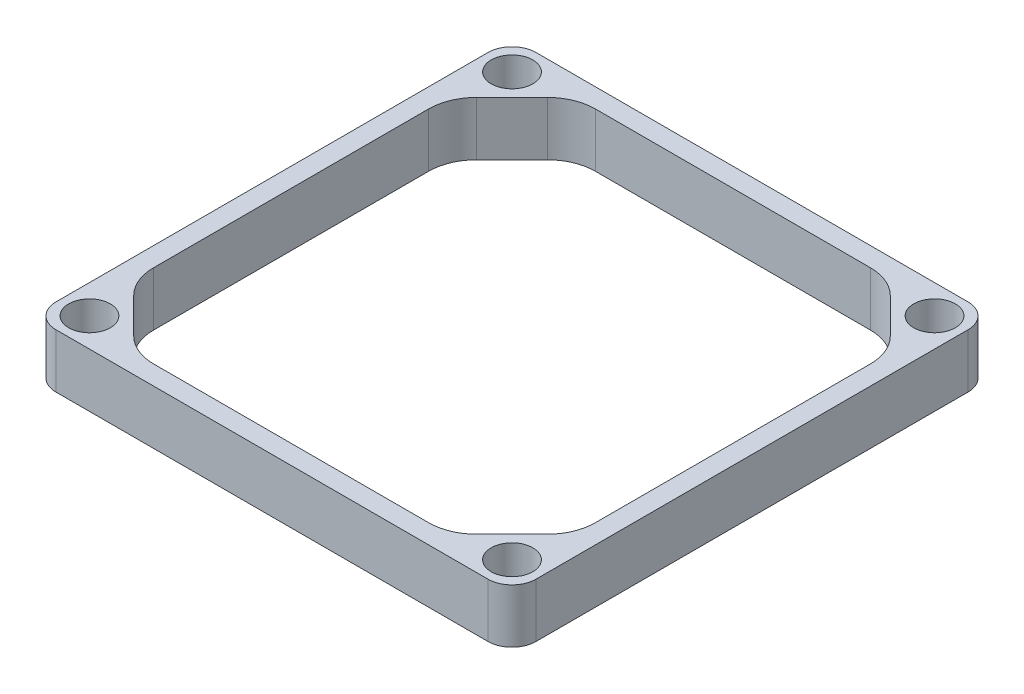
SolidWorks part; units mm, degrees
ref_plane "Front Plane" through (0, 0, 0) normal (0, 0, 1) x (1, 0, 0)
ref_plane "Top Plane" through (0, 0, 0) normal (0, 1, 0) x (1, 0, 0)
ref_plane "Right Plane" through (0, 0, 0) normal (1, 0, 0) x (0, 0, -1)
sketch "Sketch1" plane through (0, 0, 0) normal (0, 1, 0) x (1, 0, 0)
  line L1 (-57.15, 63.5) -> (57.15, 63.5)
  line L2 (-63.5, 57.15) -> (-63.5, -57.15)
  line L3 (-57.15, -63.5) -> (57.15, -63.5)
  line L4 (63.5, 57.15) -> (63.5, -57.15)
  line L5 (-49.403, 53.594) -> (49.403, 53.594) construction
  line L6 (-49.403, 53.594) -> (-49.403, -53.594) construction
  line L7 (-49.403, -53.594) -> (49.403, -53.594) construction
  line L8 (49.403, 53.594) -> (49.403, -53.594) construction
  circle A0 centre (0, 0) radius 44.45
  circle A1 centre (-57.15, 53.975) radius 3.25
  circle A2 centre (57.15, 53.975) radius 3.25
  circle A3 centre (57.15, -53.975) radius 3.25
  circle A4 centre (-57.15, -53.975) radius 3.25
  arc A5 (-63.5, -57.15) -> (-57.15, -63.5) centre (-57.15, -57.15) ccw
  arc A6 (57.15, -63.5) -> (63.5, -57.15) centre (57.15, -57.15) ccw
  arc A7 (57.15, 63.5) -> (63.5, 57.15) centre (57.15, 57.15) cw
  arc A8 (-57.15, 63.5) -> (-63.5, 57.15) centre (-57.15, 57.15) ccw
  point P21 (-63.5, -63.5)
  point P26 (63.5, 63.5)
  point P29 (-63.5, 63.5)
  dimension "D1" = 88.9
  dimension "D10" = 6.5
  dimension "D11" = 6.5
  dimension "D12" = 6.5
  dimension "D13" = 6.5
  dimension "D22" = 6.35
  dimension "D2" = 127
  dimension "D3" = 127
  dimension "D4" = 63.5
  dimension "D5" = 63.5
  dimension "D6" = 107.188
  dimension "D7" = 98.806
  dimension "D8" = 19.812
  dimension "D9" = 14.097
  dimension "D14" = 9.525
  dimension "D15" = 6.35
  dimension "D16" = 9.525
  dimension "D17" = 6.35
  dimension "D18" = 6.35
  dimension "D19" = 9.525
  dimension "D20" = 9.525
  dimension "D21" = 6.35
extrude "Boss-Extrude1" add sketch "Sketch1" along normal blind 3.175
sketch "Sketch3" plane through (0, 3.175, 0) normal (0, 1, 0) x (1, 0, 0)
  line L0 (-54.7003, 45.359) -> (-45.359, 54.7003)
  line L1 (45.359, 54.7003) -> (54.7003, 45.359)
  line L2 (54.7003, -45.359) -> (45.359, -54.7003)
  line L3 (-45.359, -54.7003) -> (-54.7003, -45.359)
  line L4 (-57.15, -63.5) -> (57.15, -63.5)
  line L5 (63.5, -57.15) -> (63.5, 57.15)
  line L6 (57.15, 63.5) -> (-57.15, 63.5)
  line L7 (-63.5, 57.15) -> (-63.5, -57.15)
  line L8 (-57.15, -63.5) -> (57.15, -63.5)
  line L9 (63.5, -57.15) -> (63.5, 57.15)
  line L10 (57.15, 63.5) -> (-57.15, 63.5)
  line L11 (-63.5, 57.15) -> (-63.5, -57.15)
  line L12 (-36.3787, 58.42) -> (36.3787, 58.42)
  line L13 (58.42, -36.3787) -> (58.42, 36.3787)
  line L14 (-36.3787, -58.42) -> (36.3787, -58.42)
  line L15 (-58.42, -36.3787) -> (-58.42, 36.3787)
  arc A0 (36.3787, 58.42) -> (45.359, 54.7003) centre (36.3787, 45.72) cw
  arc A1 (58.42, 36.3787) -> (54.7003, 45.359) centre (45.72, 36.3787) ccw
  arc A2 (58.42, -36.3787) -> (54.7003, -45.359) centre (45.72, -36.3787) cw
  arc A3 (36.3787, -58.42) -> (45.359, -54.7003) centre (36.3787, -45.72) ccw
  arc A4 (-63.5, -57.15) -> (-57.15, -63.5) centre (-57.15, -57.15) ccw
  arc A5 (57.15, -63.5) -> (63.5, -57.15) centre (57.15, -57.15) ccw
  arc A6 (63.5, 57.15) -> (57.15, 63.5) centre (57.15, 57.15) ccw
  arc A7 (-57.15, 63.5) -> (-63.5, 57.15) centre (-57.15, 57.15) ccw
  arc A8 (-63.5, -57.15) -> (-57.15, -63.5) centre (-57.15, -57.15) ccw
  arc A9 (57.15, -63.5) -> (63.5, -57.15) centre (57.15, -57.15) ccw
  arc A10 (63.5, 57.15) -> (57.15, 63.5) centre (57.15, 57.15) ccw
  arc A11 (-57.15, 63.5) -> (-63.5, 57.15) centre (-57.15, 57.15) ccw
  arc A12 (-36.3787, -58.42) -> (-45.359, -54.7003) centre (-36.3787, -45.72) cw
  arc A13 (-58.42, -36.3787) -> (-54.7003, -45.359) centre (-45.72, -36.3787) ccw
  arc A14 (-58.42, 36.3787) -> (-54.7003, 45.359) centre (-45.72, 36.3787) cw
  arc A15 (-36.3787, 58.42) -> (-45.359, 54.7003) centre (-36.3787, 45.72) ccw
  dimension "D2" = 12.7
  dimension "D3" = 72.7574
  dimension "D4" = 72.7574
  dimension "D5" = 72.7574
  dimension "D6" = 72.7574
  dimension "D7" = 135
  dimension "D8" = 135
  dimension "D9" = 135
  dimension "D10" = 135
  dimension "D11" = 180
  dimension "D12" = 180
  dimension "D13" = 180
  dimension "D14" = 13.2106
  dimension "D15" = 13.2106
  dimension "D16" = 8.7997
  dimension "D17" = 11.791
  dimension "D1" = 0
extrude "Boss-Extrude2" add sketch "Sketch3" along normal blind 25.4
hole_wizard "CBORE for M6 SHCS2" positions "Sketch8" profile "Sketch9" counterbore size "M6" standard "ANSI Metric" end condition through all
sketch "Sketch8" plane through (0, 0, 0) normal (0, -1, 0) x (-1, 0, 0)
  line L0 (57.15, -63.5) -> (-57.15, -63.5) construction
  line L1 (63.5, 57.15) -> (63.5, -57.15) construction
  line L2 (-63.5, -57.15) -> (-63.5, 57.15) construction
  line L3 (-57.15, 63.5) -> (57.15, 63.5) construction
  point P0 (-55.88, 55.88)
  point P4 (55.88, 55.88)
  point P6 (55.88, -55.88)
  point P10 (-55.88, -55.88)
  dimension "D1" = 7.62
  dimension "D2" = 7.62
  dimension "D3" = 7.62
  dimension "D4" = 7.62
  dimension "D5" = 7.62
  dimension "D6" = 7.62
  dimension "D7" = 7.62
  dimension "D8" = 7.62
sketch "Sketch9" plane through (55.88, 0, -55.88) normal (1, 0, 0) x (0, 0, -1)
  line L0 (0, 0) -> (0, 28.575)
  line L1 (0, 28.575) -> (3.5, 28.575)
  line L3 (3.5, 28.575) -> (3.5, 6)
  line L4 (3.5, 6) -> (5.5, 6)
  line L5 (5.5, 6) -> (5.5, 0)
  line L7 (5.5, 0) -> (0, 0)
  line L11 (0, -6.35) -> (0, 107.95) construction
  dimension "Thru Hole Dia." = 7
  dimension "Thru Hole Depth" = 28.575
  dimension "C'Bore Dia." = 11
  dimension "C'Bore Depth" = 6
ref_plane "Plane1" through (0, 14.2875, 0) normal (0, -1, 0) x (-1, 0, 0)
sketch "Sketch10" plane through (0, 14.2875, 0) normal (0, -1, 0) x (-1, 0, 0)
  line L1 (-98.5501, 120.0463) -> (107.7253, 120.0463)
  line L2 (-98.5501, 120.0463) -> (-98.5501, -114.3522)
  line L3 (-98.5501, -114.3522) -> (107.7253, -114.3522)
  line L4 (107.7253, 120.0463) -> (107.7253, -114.3522)
extrude "Cut-Extrude1" cut sketch "Sketch10" along normal through all
hole_wizard "CBORE for M6 SHCS3" positions "Sketch11" profile "Sketch12" counterbore size "M6" standard "ANSI Metric" end condition through all
sketch "Sketch11" plane through (0, 28.575, 0) normal (0, 1, 0) x (1, 0, 0)
  point P0 (55.88, 55.88)
  point P3 (55.88, -55.88)
  point P6 (-55.88, -55.88)
  point P9 (-55.88, 55.88)
sketch "Sketch12" plane through (55.88, 28.575, -55.88) normal (1, 0, 0) x (0, 0, 1)
  line L0 (0, 0) -> (0, 14.2875)
  line L1 (0, 14.2875) -> (3.5, 14.2875)
  line L3 (3.5, 14.2875) -> (3.5, 8.54)
  line L4 (3.5, 8.54) -> (5.5, 8.54)
  line L5 (5.5, 8.54) -> (5.5, 0)
  line L7 (5.5, 0) -> (0, 0)
  line L11 (0, -6.35) -> (0, 107.95) construction
  dimension "Thru Hole Dia." = 7
  dimension "Thru Hole Depth" = 14.2875
  dimension "C'Bore Dia." = 11
  dimension "C'Bore Depth" = 8.54
equation "\"D4@Sketch1\"=\"D3@Sketch1\"/2"
equation "\"D5@Sketch1\"=\"D2@Sketch1\"/2"
equation "\"D8@Sketch1\"=\"D2@Sketch1\"-\"D6@Sketch1\""
equation "\"D9@Sketch1\"=(\"D3@Sketch1\"-\"D7@Sketch1\")/2"
equation "\"D10@Sketch1\"=6.5/25.4"
equation "\"D11@Sketch1\"=\"D10@Sketch1\""
equation "\"D12@Sketch1\"=\"D10@Sketch1\""
equation "\"D13@Sketch1\"=\"D10@Sketch1\""
